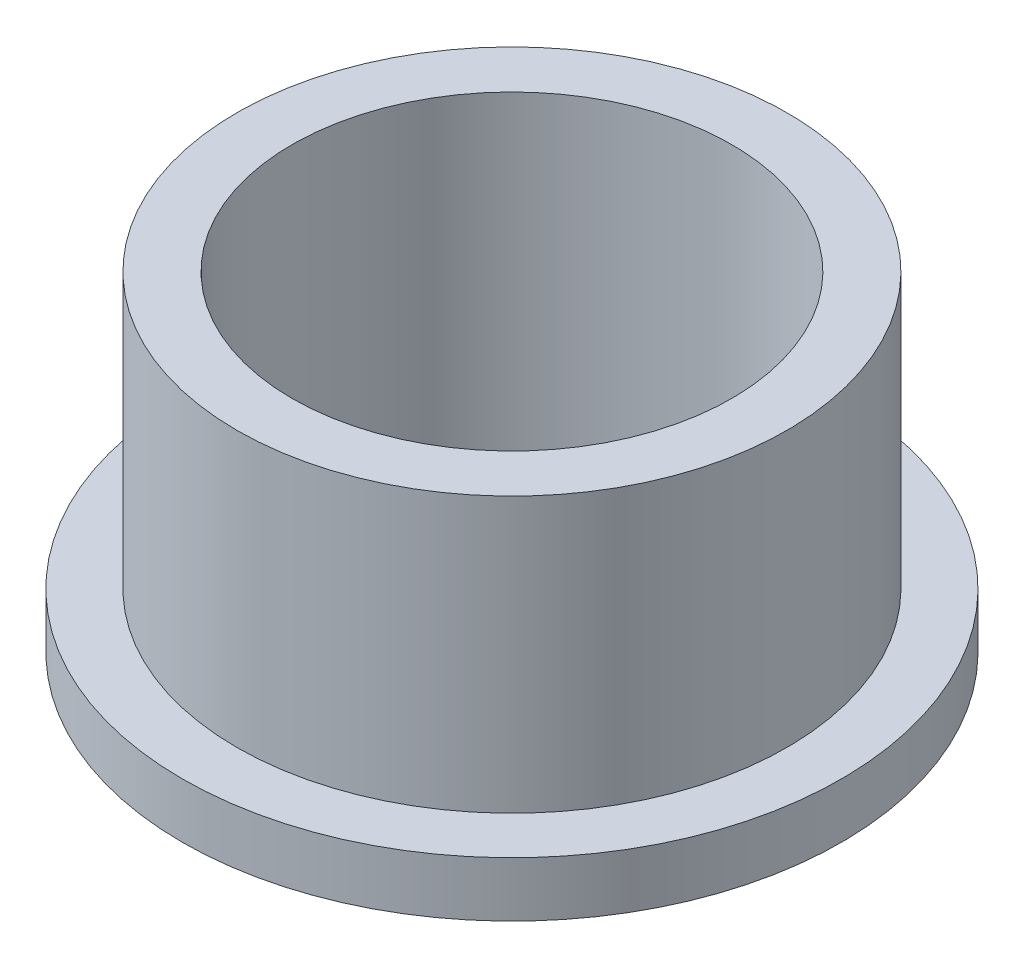
SolidWorks part; units mm, degrees
ref_plane "Front" through (0, 0, 0) normal (0, 0, 1) x (1, 0, 0)
ref_plane "Top" through (0, 0, 0) normal (0, 1, 0) x (1, 0, 0)
ref_plane "Right" through (0, 0, 0) normal (1, 0, 0) x (0, 0, -1)
sketch "Sketch1" plane through (0, 0, 0) normal (0, 1, 0) x (1, 0, 0)
  circle A0 centre (0, 0) radius 12.7102
  circle A1 centre (0, 0) radius 15.9004
  circle A2 centre (0, 0) radius 19.05
  dimension "ID" = 25.4203
  dimension "OD" = 31.8008
  dimension "FlangeOD" = 38.1
sketch "Sketch2" plane through (0, 0, 0) normal (0, 1, 0) x (1, 0, 0)
  circle A0 centre (0, 0) radius 12.7102 construction
  circle A1 centre (0, 0) radius 15.9004 construction
  circle A2 centre (0, 0) radius 12.7102
  circle A3 centre (0, 0) radius 15.9004
extrude "Boss-Extrude1" add sketch "Sketch2" along normal blind 19.05
sketch "Sketch3" plane through (0, 0, 0) normal (0, 1, 0) x (1, 0, 0)
  circle A0 centre (0, 0) radius 19.05 construction
  circle A1 centre (0, 0) radius 15.9004 construction
  circle A2 centre (0, 0) radius 19.05
  circle A3 centre (0, 0) radius 15.9004
extrude "Boss-Extrude2" add sketch "Sketch3" along normal blind 3.175
